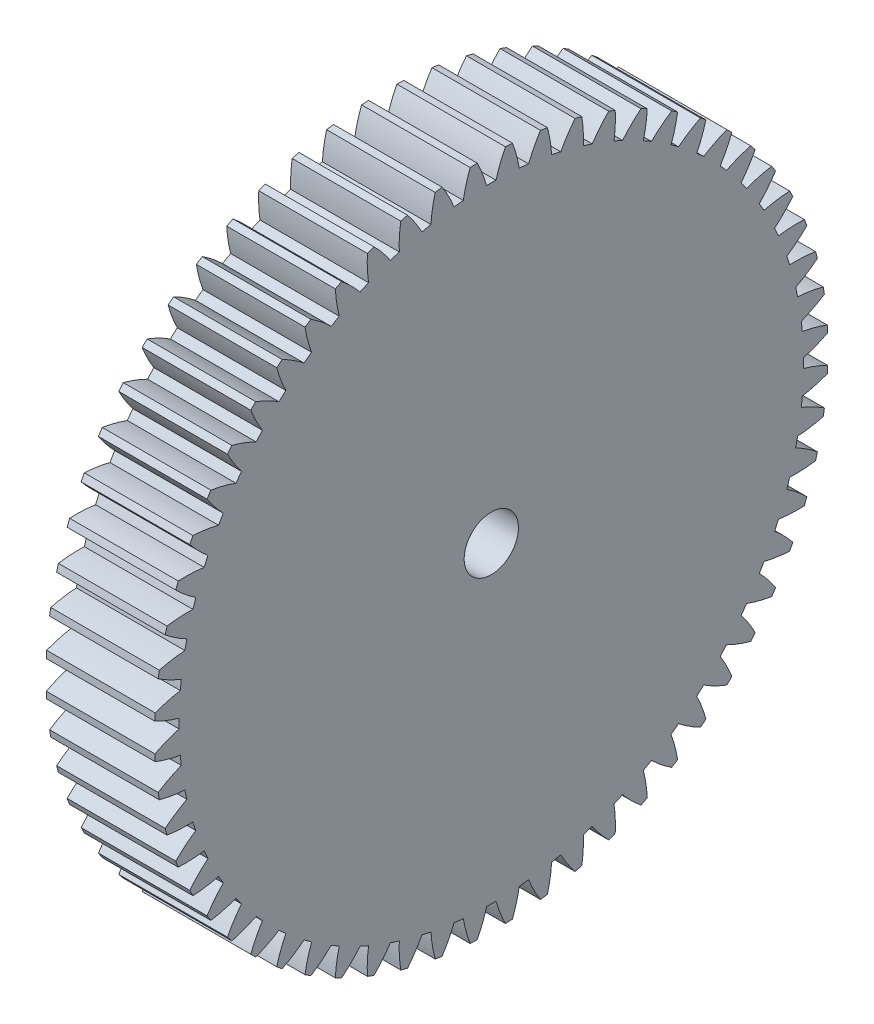
SolidWorks part; units mm, degrees
ref_plane "Plane1" through (0, 0, 0) normal (0, 0, 1) x (1, 0, 0)
ref_plane "Plane2" through (0, 0, 0) normal (0, 1, 0) x (1, 0, 0)
ref_plane "Plane3" through (0, 0, 0) normal (1, 0, 0) x (0, 0, -1)
other "Configuration Table"
sketch "HoldingSke" plane through (0, 0, 0) normal (0, 1, 0) x (1, 0, 0)
  line L0 (0, 0) -> (0.5, -0.866)
  line L1 (-15, 0) -> (100, 0) construction
  line L2 (0, 0) -> (-2.1039, 2.3779)
  line L3 (0, 0) -> (-11.863, 4.5341)
  line L4 (0, 0) -> (4.318, 7.479)
  line L5 (0, 0) -> (-46.8476, -17.4728)
  line L6 (0, 0) -> (-8.2896, -5.593)
  line L7 (-2.1039, 2.3779) -> (8.6586, 51.2059)
  line L8 (-76.2, 54.61) -> (-75.3, 54.61)
  line L9 (-71.009, 38.7566) -> (-53.1078, 45.2721)
  line L10 (-76.2, 71.12) -> (104.1128, 71.12)
  line L11 (0, 0) -> (-10, 0)
  line L12 (-76.2, 101.6) -> (-76.162, 101.6)
  line L13 (24.9733, 27.94) -> (52.9518, 28.4284)
  line L14 (24.9733, 27.94) -> (24.9743, 27.94)
  line L15 (24.9733, 27.94) -> (100.4006, 29.5858)
  line L16 (-63.627, -1) -> (-12.827, -1)
  circle A0 centre (0, 0) radius 2.5
  circle A1 centre (0, 0) radius 28.749
  circle A2 centre (0, 0) radius 37.5
  circle A3 centre (0, 0) radius 2.5
  dimension "MHD" = 57.498
  dimension "Hub_dia" = 75
  dimension "Bore" = 5
  dimension "MBD" = 5
  dimension "Num_teeth" = 60
  dimension "Pitch" = 1
  dimension "Overall_len" = 50
  dimension "Show_teeth" = 60
  dimension "Thickness" = 10
  dimension "OAL" = 50.0001
  dimension "T_dim" = 0.9
  dimension "Ap" = 20
  dimension "H" = 19.05
  dimension "Pitch_radius" = 180.3128
  dimension "Width" = 10
  dimension "Backlash" = 0.038
  dimension "Addendum_fac" = 1
  dimension "Dedendum_fac" = 1.25
  dimension "Clearance_fac" = 0.25
  dimension "Dedendum_add" = 0.001
  dimension "Module" = 1
sketch "BasProSke" plane through (0, 0, 0) normal (0, 1, 0) x (1, 0, 0)
  line L0 (-10, 0) -> (60, 0) construction
  line L1 (0, 0) -> (0, 31)
  line L2 (0, 0) -> (10, 0)
  line L3 (10, 0) -> (10, 31)
  line L4 (10, 31) -> (0, 31)
  dimension "Thickness" = 10
  dimension "Diameter" = 62
revolve "Base-Revolve" add sketch "BasProSke" angle 360 about L0
sketch "TooCutSke" plane through (0, 0, 0) normal (1, 0, 0) x (0, 0, -1)
  line L1 (0, 0) -> (0, 107) construction
  line L2 (0, 0) -> (-0.8518, 29.9879) construction
  line L3 (0, 0) -> (-3.1393, 59.9006) construction
  line L4 (-0.8518, 29.9879) -> (-1.5696, 29.9503) construction
  arc A0 (0.4302, 28.7458) -> (-0.4302, 28.7458) centre (0, 0) ccw
  arc A1 (1.3127, 30.9976) -> (-1.3127, 30.9976) centre (0, 0) ccw
  circle A2 centre (0, 0) radius 30 construction
  circle A3 centre (0, 0) radius 28.1908 construction
  arc A4 (-0.4302, 28.7458) -> (-1.3127, 30.9976) centre (-11.9871, 25.5153) ccw
  arc A5 (1.3127, 30.9976) -> (0.4302, 28.7458) centre (11.9871, 25.5153) ccw
  dimension "Root_dia" = 57.498
  dimension "Overcut_dia" = 62.0508
  dimension "Pitch_dia" = 60
  dimension "Base_dia" = 56.3816
  dimension "Flank_rad" = 12
  dimension "Half_ang" = 3
  dimension "Half_CT" = 0.7188
extrude "ToothCut" cut sketch "TooCutSke" along normal through all
fillet "Breaks" [suppressed] radius 0.02
fillet "RootFillets" [suppressed] radius 0.251
pattern_circular "TeethCuts" count 60 every 6 about axis through (-10, 0, 0) along (1, 0, 0) of "ToothCut", "RootFillets", "Breaks"
sketch "HubNeaOneSke" plane through (0, 0, 0) normal (-1, 0, 0) x (0, 0, 1)
  circle A0 centre (0, 0) radius 28.749
  dimension "Diameter" = 57.498
extrude "HubNearOne" [suppressed] add sketch "HubNeaOneSke" along normal blind 40.0001
sketch "HubNeaBotSke" plane through (0, 0, 0) normal (-1, 0, 0) x (0, 0, 1)
  circle A0 centre (0, 0) radius 28.749
  dimension "Diameter" = 57.498
extrude "HubNearBoth" [suppressed] add sketch "HubNeaBotSke" along normal blind 20
ref_plane "FarPln" through (10, 0, 0) normal (1, 0, 0) x (0, 0, -1)
sketch "HubFarSke" plane through (10, 0, 0) normal (1, 0, 0) x (0, 0, -1)
  circle A0 centre (0, 0) radius 28.749
  dimension "Diameter" = 57.498
extrude "HubFar" [suppressed] add sketch "HubFarSke" along normal blind 20
sketch "BorSke" plane through (0, 0, 0) normal (1, 0, 0) x (0, 0, -1)
  circle A0 centre (0, 0) radius 2.5
  dimension "Diameter" = 5
extrude "Bore" cut sketch "BorSke" along normal mid plane 100.0001
sketch "KeySke" plane through (0, 0, 0) normal (1, 0, 0) x (0, 0, -1)
  line L0 (-1, 0) -> (-1, 3.4)
  line L1 (-1, 3.4) -> (1, 3.4)
  line L2 (1, 3.4) -> (1, 0)
  line L3 (0, 0) -> (0, 34) construction
  line L4 (-1, 0) -> (1, 0)
  dimension "Offset" = 3.4
  dimension "Width" = 2
extrude "Keyway" [suppressed] cut sketch "KeySke" along normal mid plane 100.0001
pattern_circular "Keyway2" [suppressed] count 2 every 90 about axis through (-10, 0, 0) along (1, 0, 0)
equation "' \"Module@HoldingSke\" = 6.35"
equation "' \"Num_teeth@HoldingSke\" = 12"
equation "' \"Ap@HoldingSke\" =  20"
equation "' \"Ap@HoldingSke\" = 20"
equation "' \"Width@HoldingSke\" = 0.5 * 25.4"
equation "' \"Hub_dia@HoldingSke\"= 1 * 25.4"
equation "' \"Hub_dia@HoldingSke\" = 1 * 25.4"
equation "' \"Overall_len@HoldingSke\" = 1.0 * 25.4"
equation "' \"Bore@HoldingSke\" = 0.75 * 25.4"
equation "' \"T_dim@HoldingSke\" = 0.1 * 25.4"
equation "' \"Width@KeySke\" = 0.25 * 25.4"
equation "' \"Show_teeth@HoldingSke\" = 13"
equation "' \"Backlash@HoldingSke\" = 0.009 * 25.4"
equation "' \"Addendum_fac@HoldingSke\" = 1.0"
equation "' \"Dedendum_fac@HoldingSke\" = 1.25"
equation "' \"Dedendum_add@HoldingSke\" = 0.00005 * 25.4"
equation "' \"Clearance_fac@HoldingSke\" = 0.25"
equation "\"Pitch@HoldingSke\" = 1 / \"Module@HoldingSke\""
equation "\"Overcut_dia@TooCutSke\" = (\"Num_teeth@HoldingSke\" + 2 * \"Addendum_fac@HoldingSke\") / \"Pitch@HoldingSke\" + 0.002 * 25.4"
equation "\"Pitch_dia@TooCutSke\" = \"Num_teeth@HoldingSke\" / \"Pitch@HoldingSke\""
equation "\"Base_dia@TooCutSke\" = \"Num_teeth@HoldingSke\" / \"Pitch@HoldingSke\" * cos((\"Ap@HoldingSke\"  * 3.14159265 / 180))"
equation "\"Root_dia@TooCutSke\" = (\"Num_teeth@HoldingSke\" + 2) / \"Pitch@HoldingSke\" - 2 * (\"Addendum_fac@HoldingSke\" + \"Dedendum_fac@HoldingSke\") / \"Pitch@HoldingSke\" - \"Dedendum_add@HoldingSke\" * 2"
equation "\"Half_ang@TooCutSke\" = 180 / \"Num_teeth@HoldingSke\""
equation "\"Half_CT@TooCutSke\" = \"Num_teeth@HoldingSke\" / \"Pitch@HoldingSke\" * sin((3.14159265 / 2 / \"Num_teeth@HoldingSke\")) / 2 - 7 * \"Backlash@HoldingSke\" / 4"
equation "\"Flank_rad@TooCutSke\" = \"Num_teeth@HoldingSke\" / \"Pitch@HoldingSke\" / 5"
equation "\"Radius@RootFillets\" = \"Clearance_fac@HoldingSke\" / \"Pitch@HoldingSke\" + \"Dedendum_add@HoldingSke\""
equation "\"Break_rad@Breaks\" = 0.02 / \"Pitch@HoldingSke\""
equation "\"Thickness@HoldingSke\" = \"Width@HoldingSke\""
equation "\"OAL@HoldingSke\" = \"Thickness@HoldingSke\""
equation "\"MHD@HoldingSke\" = (\"Num_teeth@HoldingSke\" + 2) / \"Pitch@HoldingSke\" - 2 * (\"Addendum_fac@HoldingSke\" + \"Dedendum_fac@HoldingSke\")  / \"Pitch@HoldingSke\" - \"Dedendum_add@HoldingSke\" * 2"
equation "\"MBD@HoldingSke\" = (\"Num_teeth@HoldingSke\" + 2) / \"Pitch@HoldingSke\" - 2 * (\"Addendum_fac@HoldingSke\" + \"Dedendum_fac@HoldingSke\")  / \"Pitch@HoldingSke\" - \"Dedendum_add@HoldingSke\" * 2 - 0.002 * 25.4"
equation "\"MHD@HoldingSke\" = ((sgn( \"MHD@HoldingSke\" - \"Hub_dia@HoldingSke\" )-1)*( \"MHD@HoldingSke\" - \"Hub_dia@HoldingSke\" ))/-2+ \"Hub_dia@HoldingSke\""
equation "\"MBD@HoldingSke\" = ((sgn( \"MBD@HoldingSke\" - \"Bore@HoldingSke\" )-1)*( \"MBD@HoldingSke\" - \"Bore@HoldingSke\" ))/-2+ \"Bore@HoldingSke\""
equation "\"OAL@HoldingSke\" = ((sgn( \"OAL@HoldingSke\" - \"Overall_len@HoldingSke\" )+1)*( \"OAL@HoldingSke\" - \"Overall_len@HoldingSke\" ))/2 + \"Overall_len@HoldingSke\" + 0.000002 * 25.4"
equation "\"Num_teeth@TeethCuts\" = int( \"Show_teeth@HoldingSke\" ) + 1"
equation "\"Num_teeth@TeethCuts\" = ((sgn( \"Num_teeth@TeethCuts\" - \"Num_teeth@HoldingSke\" )-1)*( \"Num_teeth@TeethCuts\" - \"Num_teeth@HoldingSke\" ))/-2+ \"Num_teeth@HoldingSke\""
equation "\"Num_teeth@TeethCuts\" = ((sgn( \"Num_teeth@TeethCuts\" - 2.0)+1)*( \"Num_teeth@TeethCuts\" - 2.0))/2 +2.0"
equation "\"Angle@TeethCuts\" = 360.0 / \"Num_teeth@HoldingSke\""
equation "\"Diameter@BasProSke\" = (\"Num_teeth@HoldingSke\" + 2 * \"Addendum_fac@HoldingSke\") / \"Pitch@HoldingSke\""
equation "\"Thickness@BasProSke\"  = \"Thickness@HoldingSke\""
equation "' \"Fillet_rad@BasProSke\" =  \"Thickness@HoldingSke\" * 0.05"
equation "' \"Fillet_rad@BasProSke\" = \"Thickness@HoldingSke\" * 0.05"
equation "\"MHD@HoldingSke\" = ((sgn( \"MHD@HoldingSke\" - \"Root_dia@TooCutSke\" )-1)*( \"MHD@HoldingSke\" - \"Root_dia@TooCutSke\" ))/-2+ \"Root_dia@TooCutSke\""
equation "\"Diameter@HubNeaOneSke\" = \"MHD@HoldingSke\""
equation "\"Length@HubNearOne\" = \"OAL@HoldingSke\" - \"Thickness@BasProSke\""
equation "\"Diameter@HubNeaBotSke\" = \"MHD@HoldingSke\""
equation "\"Length@HubNearBoth\" = ( \"OAL@HoldingSke\" - \"Thickness@BasProSke\" ) / 2.0"
equation "\"Thickness@FarPln\" = \"Thickness@BasProSke\""
equation "\"Diameter@HubFarSke\" = \"MHD@HoldingSke\""
equation "\"Length@HubFar\" = ( \"OAL@HoldingSke\" - \"Thickness@BasProSke\" ) / 2.0"
equation "\"Diameter@BorSke\" = \"MBD@HoldingSke\""
equation "\"D1@Bore\" = \"OAL@HoldingSke\" * 2.0"
equation "\"D1@Keyway\" = \"OAL@HoldingSke\" * 2.0"
equation "\"Offset@KeySke\" = \"T_dim@HoldingSke\" + \"MBD@HoldingSke\" / 2.0"
